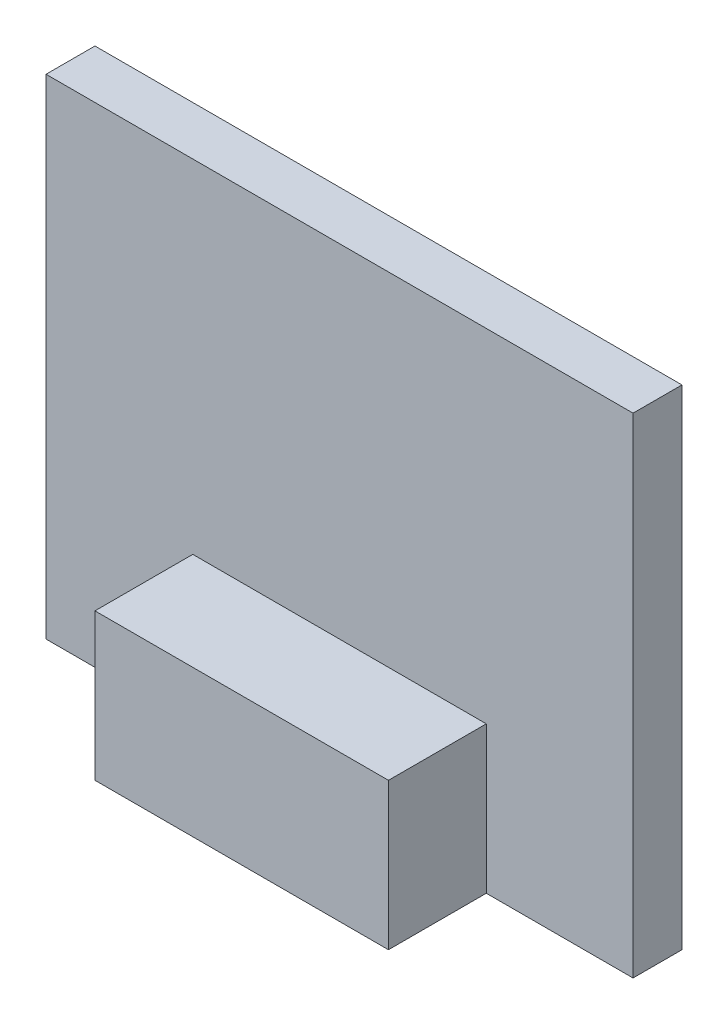
SolidWorks part; units mm, degrees
material "Delrin 2700 NC010, Low Viscosity Acetal Copolymer (SS)"
ref_plane "Front Plane" through (0, 0, 0) normal (0, 0, 1) x (1, 0, 0)
ref_plane "Top Plane" through (0, 0, 0) normal (0, 1, 0) x (1, 0, 0)
ref_plane "Right Plane" through (0, 0, 0) normal (1, 0, 0) x (0, 0, -1)
sketch "Sketch1" plane through (0, 0, 0) normal (0, 0, 1) x (1, 0, 0)
  line L0 (-38.1, 31.75) -> (38.1, -31.75) construction
  line L1 (-38.1, 31.75) -> (38.1, 31.75)
  line L2 (-38.1, 31.75) -> (-38.1, -31.75)
  line L3 (-38.1, -31.75) -> (38.1, -31.75)
  line L4 (38.1, 31.75) -> (38.1, -31.75)
  dimension "D1" = 63.5
  dimension "D2" = 76.2
extrude "Boss-Extrude1" add sketch "Sketch1" along normal blind 6.35
sketch "Sketch2" plane through (0, 0, 6.35) normal (0, 0, 1) x (1, 0, 0)
  line L0 (-38.1, -31.75) -> (38.1, -31.75) construction
  line L1 (-19.05, -12.7) -> (19.05, -12.7)
  line L2 (-19.05, -12.7) -> (-19.05, -31.75)
  line L3 (-19.05, -31.75) -> (19.05, -31.75)
  line L4 (19.05, -12.7) -> (19.05, -31.75)
  line L5 (19.05, -12.7) -> (38.1, -12.7) construction
  line L6 (38.1, -31.75) -> (38.1, 31.75) construction
  line L7 (-19.05, -12.7) -> (-38.1, -12.7) construction
  line L8 (-38.1, 31.75) -> (-38.1, -31.75) construction
  dimension "D1" = 19.05
  dimension "D2" = 38.1
extrude "Boss-Extrude2" add sketch "Sketch2" along normal blind 12.7
